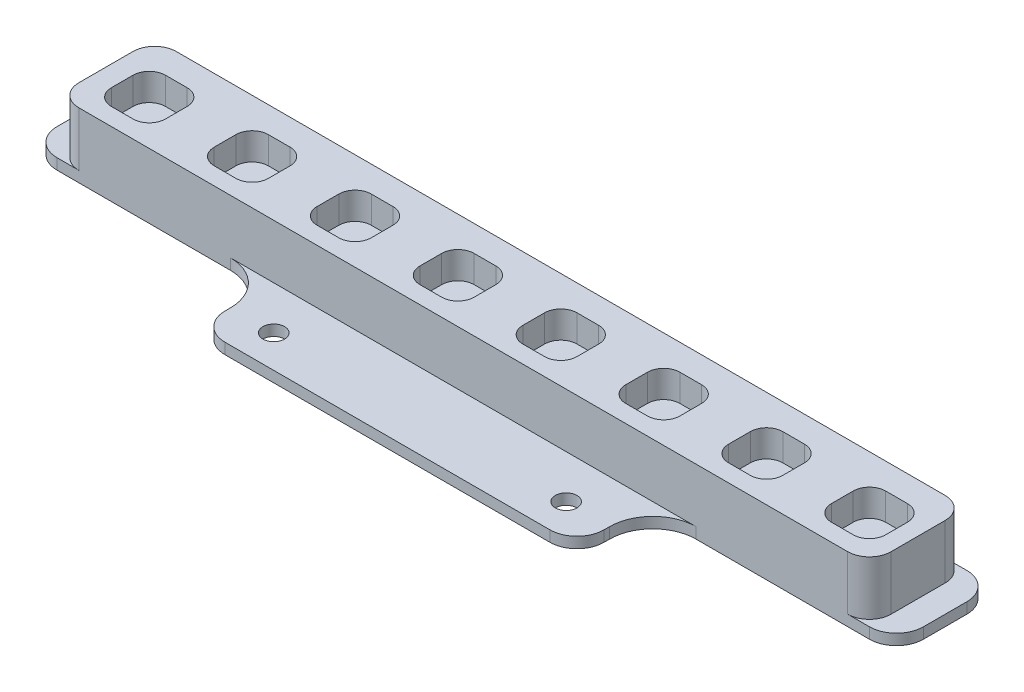
SolidWorks part; units mm, degrees
ref_plane "前视基准面" through (0, 0, 0) normal (0, 0, 1) x (1, 0, 0)
ref_plane "上视基准面" through (0, 0, 0) normal (0, 1, 0) x (1, 0, 0)
ref_plane "右视基准面" through (0, 0, 0) normal (1, 0, 0) x (0, 0, -1)
sketch "草图1" plane through (0, 0, 0) normal (0, 1, 0) x (1, 0, 0)
  line L0 (-55, 0) -> (55, 0) construction
  line L1 (-75, 32) -> (75, 32)
  line L2 (-80, 27) -> (-80, 19)
  line L3 (-30, 0) -> (30, 0)
  line L4 (80, 27) -> (80, 19)
  line L5 (0, -55) -> (0, 55) construction
  line L6 (-75, 14) -> (-43, 14)
  line L7 (-35, 6) -> (-35, 5)
  line L8 (75, 14) -> (43, 14)
  line L9 (35, 6) -> (35, 5)
  circle A0 centre (-27, 6) radius 2
  circle A1 centre (27, 6) radius 2
  arc A2 (35, 5) -> (30, 0) centre (30, 5) cw
  arc A3 (75, 14) -> (80, 19) centre (75, 19) ccw
  arc A4 (75, 32) -> (80, 27) centre (75, 27) cw
  arc A5 (-75, 32) -> (-80, 27) centre (-75, 27) ccw
  arc A6 (-75, 14) -> (-80, 19) centre (-75, 19) cw
  arc A7 (-35, 5) -> (-30, 0) centre (-30, 5) ccw
  arc A8 (43, 14) -> (35, 6) centre (43, 6) ccw
  arc A9 (-43, 14) -> (-35, 6) centre (-43, 6) cw
  point P18 (35, 0)
  point P23 (80, 32)
  point P26 (-80, 32)
  point P31 (-35, 0)
  point P36 (-35, 14)
  dimension "D7" = 4
  dimension "D8" = 4
  dimension "D13" = 5
  dimension "D14" = 8
  dimension "D1" = 160
  dimension "D2" = 54
  dimension "D3" = 80
  dimension "D4" = 32
  dimension "D5" = 18
  dimension "D6" = 35
  dimension "D9" = 26
  dimension "D10" = 26
  dimension "D11" = 27
  dimension "D12" = 70
extrude "凸台-拉伸1" add sketch "草图1" along normal blind 2
sketch "草图2" plane through (0, 2, 0) normal (0, 1, 0) x (1, 0, 0)
  line L0 (-75, 14) -> (-43, 14) construction
  line L1 (-71, 14) -> (71, 14)
  line L2 (-75, 18) -> (-75, 28)
  line L3 (-71, 32) -> (71, 32)
  line L4 (75, 18) -> (75, 28)
  arc A0 (71, 32) -> (75, 28) centre (71, 28) cw
  arc A1 (71, 14) -> (75, 18) centre (71, 18) ccw
  arc A2 (-75, 28) -> (-71, 32) centre (-71, 28) cw
  arc A3 (-71, 14) -> (-75, 18) centre (-71, 18) cw
  point P4 (-75, 32)
  point P11 (75, 32)
  point P16 (-75, 32)
  dimension "D1" = 4
extrude "凸台-拉伸2" add sketch "草图2" along normal blind 10
sketch "草图3" plane through (0, 12, 0) normal (0, 1, 0) x (1, 0, 0)
  line L0 (-49.2009, 17.2113) -> (-45.2009, 17.2113)
  line L1 (-68.2009, 17.2113) -> (-64.2009, 17.2113)
  line L2 (-71.2009, 20.2113) -> (-71.2009, 24.2113)
  line L3 (-68.2009, 27.2113) -> (-64.2009, 27.2113)
  line L4 (-61.2009, 20.2113) -> (-61.2009, 24.2113)
  line L5 (-52.2009, 20.2113) -> (-52.2009, 24.2113)
  line L6 (-49.2009, 27.2113) -> (-45.2009, 27.2113)
  line L7 (-42.2009, 20.2113) -> (-42.2009, 24.2113)
  line L8 (-30.2009, 17.2113) -> (-26.2009, 17.2113)
  line L9 (-33.2009, 20.2113) -> (-33.2009, 24.2113)
  line L10 (-30.2009, 27.2113) -> (-26.2009, 27.2113)
  line L11 (-23.2009, 20.2113) -> (-23.2009, 24.2113)
  line L12 (-11.2009, 17.2113) -> (-7.2009, 17.2113)
  line L13 (-14.2009, 20.2113) -> (-14.2009, 24.2113)
  line L14 (-11.2009, 27.2113) -> (-7.2009, 27.2113)
  line L15 (-4.2009, 20.2113) -> (-4.2009, 24.2113)
  line L16 (7.7991, 17.2113) -> (11.7991, 17.2113)
  line L17 (4.7991, 20.2113) -> (4.7991, 24.2113)
  line L18 (7.7991, 27.2113) -> (11.7991, 27.2113)
  line L19 (14.7991, 20.2113) -> (14.7991, 24.2113)
  line L20 (26.7991, 17.2113) -> (30.7991, 17.2113)
  line L21 (23.7991, 20.2113) -> (23.7991, 24.2113)
  line L22 (26.7991, 27.2113) -> (30.7991, 27.2113)
  line L23 (33.7991, 20.2113) -> (33.7991, 24.2113)
  line L24 (45.7991, 17.2113) -> (49.7991, 17.2113)
  line L25 (42.7991, 20.2113) -> (42.7991, 24.2113)
  line L26 (45.7991, 27.2113) -> (49.7991, 27.2113)
  line L27 (52.7991, 20.2113) -> (52.7991, 24.2113)
  line L28 (64.7991, 17.2113) -> (68.7991, 17.2113)
  line L29 (61.7991, 20.2113) -> (61.7991, 24.2113)
  line L30 (64.7991, 27.2113) -> (68.7991, 27.2113)
  line L31 (71.7991, 20.2113) -> (71.7991, 24.2113)
  arc A0 (-71.2009, 24.2113) -> (-68.2009, 27.2113) centre (-68.2009, 24.2113) cw
  arc A1 (-64.2009, 27.2113) -> (-61.2009, 24.2113) centre (-64.2009, 24.2113) cw
  arc A2 (-64.2009, 17.2113) -> (-61.2009, 20.2113) centre (-64.2009, 20.2113) ccw
  arc A3 (-68.2009, 17.2113) -> (-71.2009, 20.2113) centre (-68.2009, 20.2113) cw
  arc A4 (-52.2009, 24.2113) -> (-49.2009, 27.2113) centre (-49.2009, 24.2113) cw
  arc A5 (-45.2009, 27.2113) -> (-42.2009, 24.2113) centre (-45.2009, 24.2113) cw
  arc A6 (-45.2009, 17.2113) -> (-42.2009, 20.2113) centre (-45.2009, 20.2113) ccw
  arc A7 (-49.2009, 17.2113) -> (-52.2009, 20.2113) centre (-49.2009, 20.2113) cw
  arc A8 (-33.2009, 24.2113) -> (-30.2009, 27.2113) centre (-30.2009, 24.2113) cw
  arc A9 (-26.2009, 27.2113) -> (-23.2009, 24.2113) centre (-26.2009, 24.2113) cw
  arc A10 (-26.2009, 17.2113) -> (-23.2009, 20.2113) centre (-26.2009, 20.2113) ccw
  arc A11 (-30.2009, 17.2113) -> (-33.2009, 20.2113) centre (-30.2009, 20.2113) cw
  arc A12 (-14.2009, 24.2113) -> (-11.2009, 27.2113) centre (-11.2009, 24.2113) cw
  arc A13 (-7.2009, 27.2113) -> (-4.2009, 24.2113) centre (-7.2009, 24.2113) cw
  arc A14 (-7.2009, 17.2113) -> (-4.2009, 20.2113) centre (-7.2009, 20.2113) ccw
  arc A15 (-11.2009, 17.2113) -> (-14.2009, 20.2113) centre (-11.2009, 20.2113) cw
  arc A16 (4.7991, 24.2113) -> (7.7991, 27.2113) centre (7.7991, 24.2113) cw
  arc A17 (11.7991, 27.2113) -> (14.7991, 24.2113) centre (11.7991, 24.2113) cw
  arc A18 (11.7991, 17.2113) -> (14.7991, 20.2113) centre (11.7991, 20.2113) ccw
  arc A19 (7.7991, 17.2113) -> (4.7991, 20.2113) centre (7.7991, 20.2113) cw
  arc A20 (23.7991, 24.2113) -> (26.7991, 27.2113) centre (26.7991, 24.2113) cw
  arc A21 (30.7991, 27.2113) -> (33.7991, 24.2113) centre (30.7991, 24.2113) cw
  arc A22 (30.7991, 17.2113) -> (33.7991, 20.2113) centre (30.7991, 20.2113) ccw
  arc A23 (26.7991, 17.2113) -> (23.7991, 20.2113) centre (26.7991, 20.2113) cw
  arc A24 (42.7991, 24.2113) -> (45.7991, 27.2113) centre (45.7991, 24.2113) cw
  arc A25 (49.7991, 27.2113) -> (52.7991, 24.2113) centre (49.7991, 24.2113) cw
  arc A26 (49.7991, 17.2113) -> (52.7991, 20.2113) centre (49.7991, 20.2113) ccw
  arc A27 (45.7991, 17.2113) -> (42.7991, 20.2113) centre (45.7991, 20.2113) cw
  arc A28 (61.7991, 24.2113) -> (64.7991, 27.2113) centre (64.7991, 24.2113) cw
  arc A29 (68.7991, 27.2113) -> (71.7991, 24.2113) centre (68.7991, 24.2113) cw
  arc A30 (68.7991, 17.2113) -> (71.7991, 20.2113) centre (68.7991, 20.2113) ccw
  arc A31 (64.7991, 17.2113) -> (61.7991, 20.2113) centre (64.7991, 20.2113) cw
  point P6 (-71.2009, 27.2113)
  point P9 (-61.2009, 27.2113)
  point P14 (-71.2009, 17.2113)
  dimension "D3" = 3
  dimension "D1" = 10
  dimension "D2" = 10
  dimension "D4" = 8
extrude "切除-拉伸1" cut sketch "草图3" against normal blind 5
